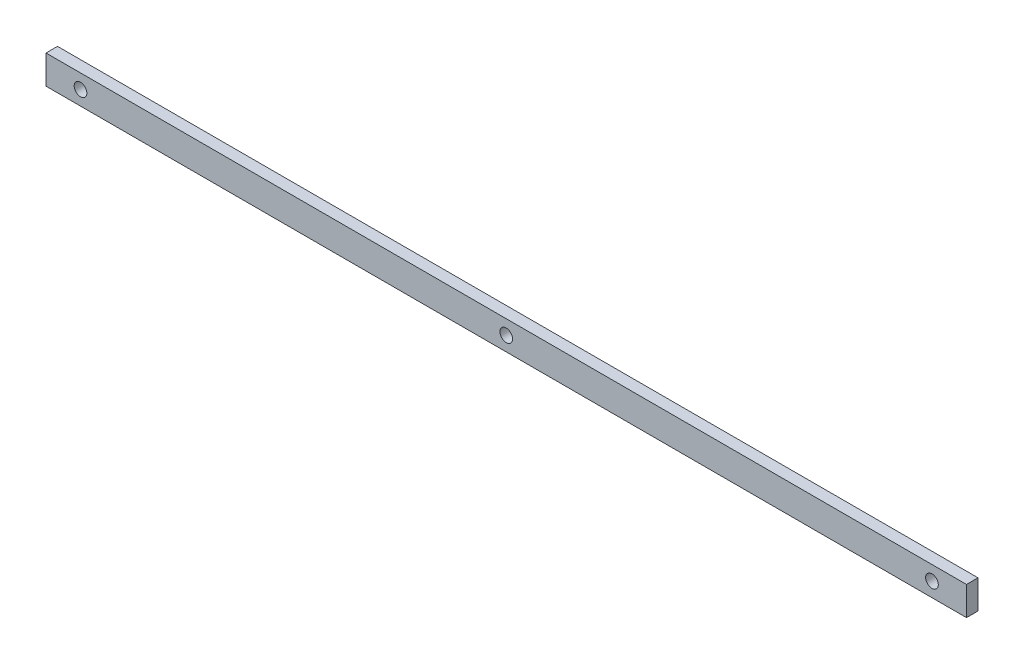
SolidWorks part; units mm, degrees
ref_plane "Front Plane" through (0, 0, 0) normal (0, 0, 1) x (1, 0, 0)
ref_plane "Top Plane" through (0, 0, 0) normal (0, 1, 0) x (1, 0, 0)
ref_plane "Right Plane" through (0, 0, 0) normal (1, 0, 0) x (0, 0, -1)
sketch "Sketch1" plane through (0, 0, 0) normal (0, 0, 1) x (1, 0, 0)
  line L1 (-400, 12.5) -> (400, 12.5)
  line L2 (-400, 12.5) -> (-400, -12.5)
  line L3 (-400, -12.5) -> (400, -12.5)
  line L4 (400, 12.5) -> (400, -12.5)
  line L5 (-400, 12.5) -> (400, -12.5) construction
  line L6 (-400, -12.5) -> (400, 12.5) construction
  point P0 (0, 0)
  dimension "D1" = 800
  dimension "D2" = 25
extrude "Boss-Extrude1" add sketch "Sketch1" along normal blind 10
sketch "Sketch2" plane through (0, 0, 0) normal (0, 0, 1) x (1, 0, 0)
  line L0 (400, -12.5) -> (400, 12.5) construction
  line L1 (400, 12.5) -> (-400, 12.5) construction
  line L2 (-400, 12.5) -> (-400, -12.5) construction
  circle A0 centre (370, 0) radius 5.5
  circle A1 centre (-370, 0) radius 5.5
  circle A2 centre (0, 0) radius 5.5
  dimension "D1" = 11
  dimension "D2" = 30
  dimension "D3" = 12.5
  dimension "D4" = 11
  dimension "D5" = 30
  dimension "D6" = 11
extrude "Cut-Extrude1" cut sketch "Sketch2" along normal blind 20
